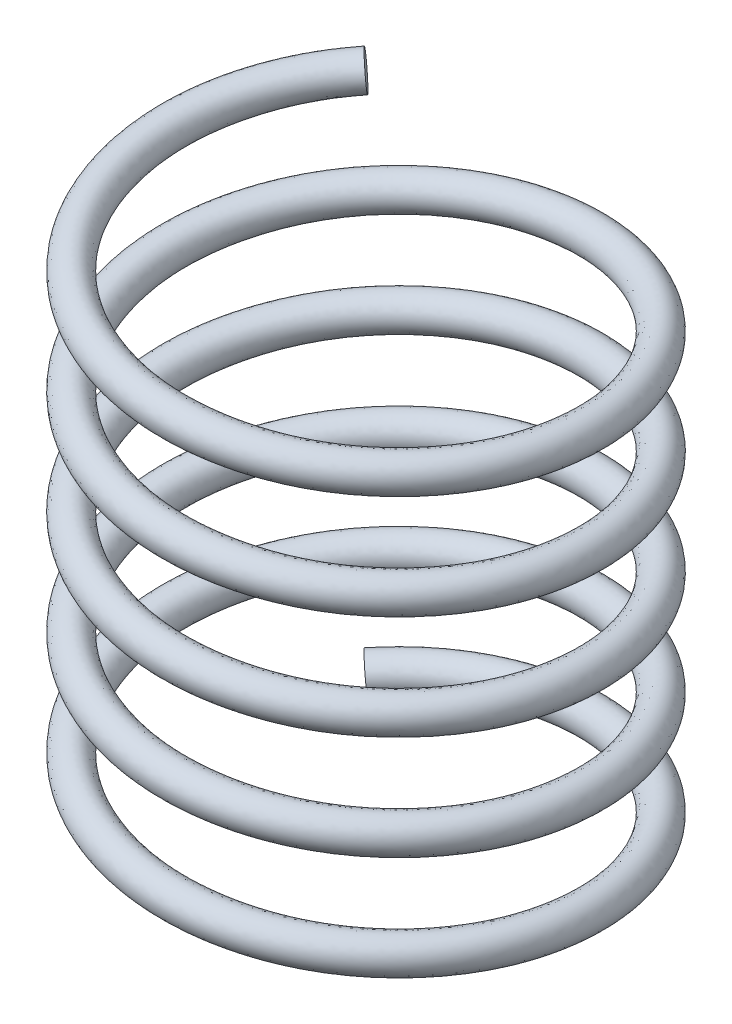
SolidWorks part; units mm, degrees
material "Plain Carbon Steel"
ref_plane "Front Plane" through (0, 0, 0) normal (0, 0, 1) x (1, 0, 0)
ref_plane "Top Plane" through (0, 0, 0) normal (0, 1, 0) x (1, 0, 0)
ref_plane "Right Plane" through (0, 0, 0) normal (1, 0, 0) x (0, 0, -1)
sketch "Sketch1" plane through (0, 0, 0) normal (0, 0, 1) x (1, 0, 0)
  line L0 (0, 0) -> (0, 15) construction
sketch "Sketch2" plane through (0, 0, 0) normal (0, 1, 0) x (1, 0, 0)
  circle A0 centre (0, 0) radius 6
  dimension "D1" = 12
curve "Helix/Spiral1" pitch 3 height 15 turns 5
ref_plane "Plane2" through (-4.2426, 0, -4.2426) normal (0.7049, 0.0793, -0.7049) x (-0.7093, 0.0788, -0.7005)
sketch "Sketch4" plane through (-4.2426, 0, -4.2426) normal (0.7049, 0.0793, -0.7049) x (-0.7093, 0.0788, -0.7005)
  circle A0 centre (0.002, 0.0008) radius 0.5
  point P2 (0, 0)
  point P3 (0.002, 0.0008)
sweep "Sweep2" add profiles "Sketch4" path "Helix/Spiral1"
sketch "Sketch5" plane through (0, 0, 0) normal (0, 1, 0) x (1, 0, 0)
  circle A0 centre (0, 0) radius 9.5208 construction
